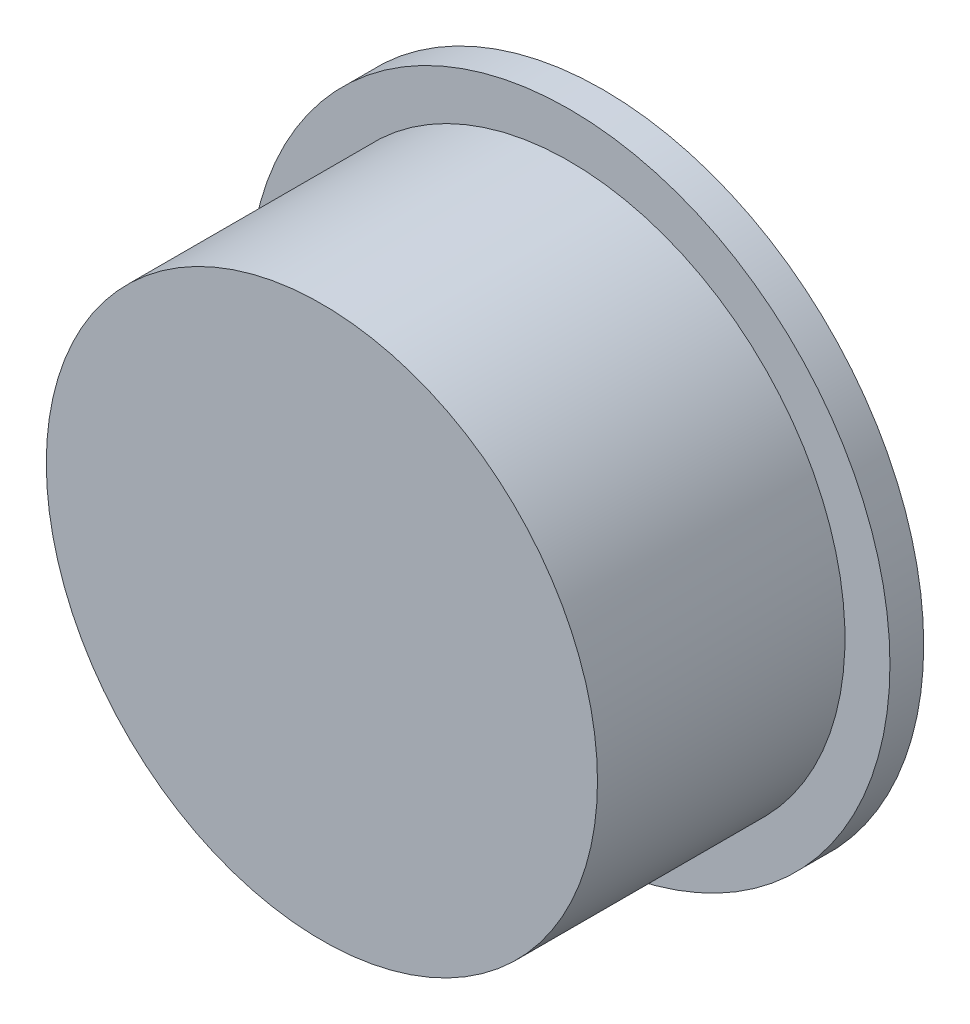
SolidWorks part; units mm, degrees
ref_plane "Front Plane" through (0, 0, 0) normal (0, 0, 1) x (1, 0, 0)
ref_plane "Top Plane" through (0, 0, 0) normal (0, 1, 0) x (1, 0, 0)
ref_plane "Right Plane" through (0, 0, 0) normal (1, 0, 0) x (0, 0, -1)
sketch "Sketch1" plane through (0, 0, 0) normal (0, 0, 1) x (1, 0, 0)
  circle A0 centre (-8.5227, 9.1777) radius 24.5
  circle A1 centre (-8.5227, 9.1777) radius 22.5
  dimension "D1" = 49
  dimension "D2" = 2
extrude "Boss-Extrude1" add sketch "Sketch1" against normal blind 15 and the other way blind 10
sketch "Sketch2" plane through (0, 0, 10) normal (0, 0, 1) x (1, 0, 0)
  circle A0 centre (-8.5227, 9.1777) radius 22.7359
extrude "Boss-Extrude2" add sketch "Sketch2" against normal blind 2
sketch "Sketch3" plane through (0, 0, -15) normal (0, 0, -1) x (-1, 0, 0)
  line L0 (31.0227, 9.1777) -> (-13.9773, 9.1777) construction
  line L1 (8.5227, 19.1777) -> (8.5227, -0.8223) construction
  line L2 (16.5227, 14.1777) -> (31.0227, 14.1777)
  line L3 (16.5227, 14.1777) -> (16.5227, 4.1777)
  line L4 (16.5227, 4.1777) -> (31.0227, 4.1777)
  line L5 (31.0227, 14.1777) -> (31.0227, 4.1777)
  line L6 (0.5227, 4.1777) -> (-13.9773, 4.1777)
  line L7 (-13.9773, 14.1777) -> (-13.9773, 4.1777)
  line L8 (0.5227, 14.1777) -> (-13.9773, 14.1777)
  line L9 (0.5227, 14.1777) -> (0.5227, 4.1777)
  circle A0 centre (8.5227, 9.1777) radius 22.5 construction
  circle A1 centre (8.5227, 9.1777) radius 10
  point P13 (31.0227, 9.1777)
  circle M6 centre (8.5227, 9.1777) radius 22.5
  dimension "D1" = 20
  dimension "D2" = 5
  dimension "D3" = 5
  dimension "D4" = 8
extrude "Boss-Extrude3" add sketch "Sketch3" against normal blind 2 contours A1 L4 L2 M6 | L4 A1 L2 L3 | L2 A1 L8 L9 L6 L4 L3 | L8 A1 L6 L9 | A1 L8 L6 M6
sketch "Sketch4" plane through (0, 0, -15) normal (0, 0, -1) x (-1, 0, 0)
  circle A0 centre (8.5227, 9.1777) radius 24.5 construction
  circle A1 centre (8.5227, 9.1777) radius 24.5
  circle A3 centre (8.5227, 9.1777) radius 28.5
  point P5 (8.5227, 9.5461)
  point P6 (8.5227, 9.5461)
  point P7 (8.5227, 9.5461)
  point P8 (8.5227, 9.5461)
  dimension "D1" = 4
  dimension "D2" = 0
  dimension "D3" = 0
extrude "Boss-Extrude4" add sketch "Sketch4" against normal blind 3 from offset 0
